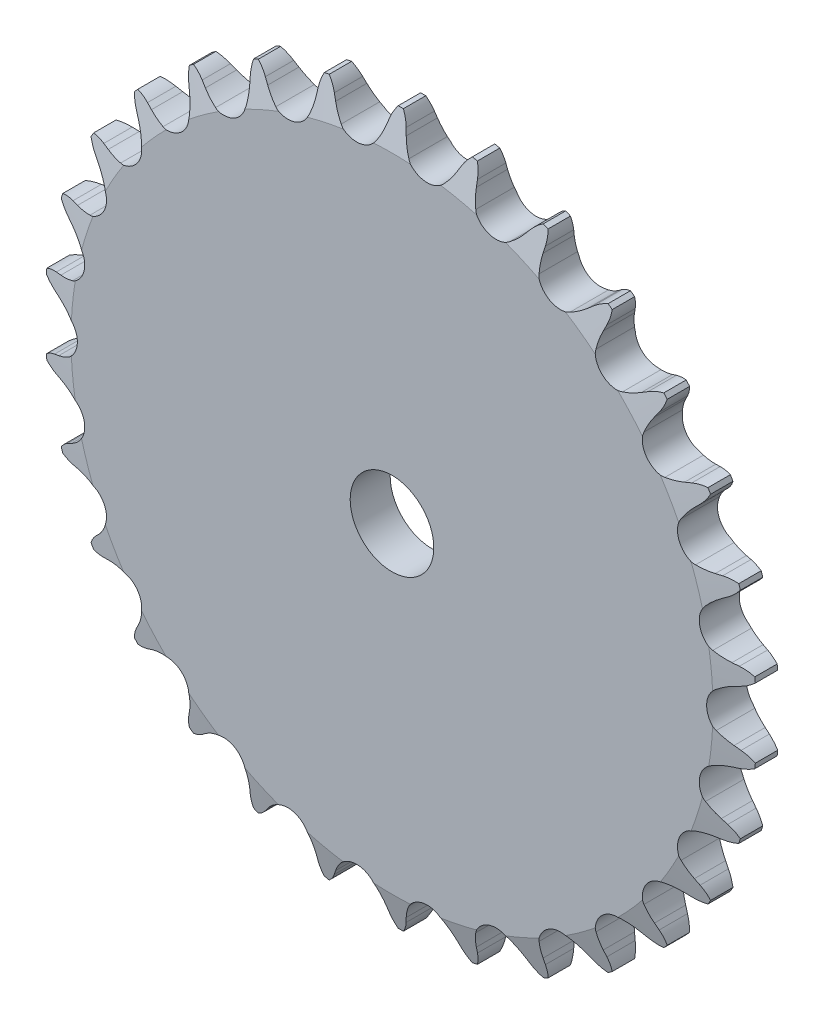
SolidWorks part; units mm, degrees
ref_plane "Front Plane" through (0, 0, 0) normal (0, 0, 1) x (1, 0, 0)
ref_plane "Top Plane" through (0, 0, 0) normal (0, 1, 0) x (1, 0, 0)
ref_plane "Right Plane" through (0, 0, 0) normal (1, 0, 0) x (0, 0, -1)
sketch "Sketch0" plane through (0, 0, 0) normal (0, 0, 1) x (1, 0, 0)
  line L0 (6.35, -60.4162) -> (0, 0) construction
  line L1 (0, 0) -> (18.7725, -57.7757) construction
  line L2 (0, 0) -> (-6.35, -60.4162) construction
  line L3 (6.35, -60.4162) -> (18.7725, -57.7757) construction
  line L4 (6.35, -60.4162) -> (-6.35, -60.4162) construction
  line L5 (11.4455, -61.0259) -> (10.9552, -60.0581)
  line L6 (6.35, -60.4162) -> (0, -61.0836) construction
  line L7 (1.4926, -62.072) -> (1.771, -61.0234)
  line L8 (0, -60.4162) -> (0, -64.2262) construction
  line L9 (9.2903, -57.6744) -> (1.7133, -64.74) construction
  line L10 (0, 0) -> (0, -60.4162) construction
  line L11 (10.9552, -60.0581) -> (1.7133, -64.74) construction
  line L12 (0, -64.2262) -> (0, -64.7904) construction
  line L13 (17.2023, -58.1095) -> (11.4455, -61.0259) construction
  circle A0 centre (0, 0) radius 64.2262 construction
  circle A1 centre (0, 0) radius 60.749 construction
  arc A2 (-5.25, -66.8497) -> (19.0341, -64.2974) centre (0, 0) ccw
  circle A3 centre (0, 0) radius 64.7904 construction
  circle A4 centre (6.35, -60.4162) radius 3.9624 construction
  arc A7 (9.2903, -57.6744) -> (2.9039, -58.3456) centre (6.35, -60.4162) ccw
  circle A8 centre (6.35, -60.4162) radius 4.0203 construction
  arc A9 (11.4455, -61.0259) -> (19.0341, -64.2974) centre (17.2023, -58.1095) ccw
  arc A10 (10.9552, -60.0581) -> (9.2903, -57.6744) centre (1.7133, -64.74) ccw
  arc A11 (1.4926, -62.072) -> (-5.25, -66.8497) centre (-4.7447, -60.4162) cw
  arc A12 (1.771, -61.0234) -> (2.9039, -58.3456) centre (11.7843, -63.6815) cw
  dimension "D1" = 4.0203
  dimension "Dr" = 7.9248
  dimension "Ds" = 8.0406
  dimension "R" = 4.0203
  dimension "Pitch" = 12.7
  dimension "A" = 37
  dimension "360/N" = 12
  dimension "B" = 16.133
  dimension "ab" = 11.0947
  dimension "J" = 3.81
  dimension "ac" = 6.3398
sketch "Sketch1" plane through (0, 0, 0) normal (1, 0, 0) x (0, 0, -1)
  line L0 (3.6068, 0) -> (-3.6068, 0)
  line L1 (-3.6068, 0) -> (-3.6068, 57.8762)
  line L2 (-3.6068, 57.8762) -> (-2.0193, 64.2262)
  line L3 (-2.0193, 64.2262) -> (2.0193, 64.2262)
  line L4 (2.0193, 64.2262) -> (3.6068, 57.8762)
  line L5 (3.6068, 57.8762) -> (3.6068, 0)
  line L7 (0, 64.2262) -> (0, 0) construction
  line L8 (-3.6068, 57.8762) -> (3.6068, 57.8762) construction
  line L9 (0, 64.2262) -> (0, -64.2262) construction
  line L10 (-3.6068, 57.8762) -> (-3.6068, 64.2262) construction
  line L11 (-3.6068, 64.2262) -> (-2.0193, 64.2262) construction
  line L12 (2.0193, 64.2262) -> (3.6068, 64.2262) construction
  line L13 (3.6068, 64.2262) -> (3.6068, 57.8762) construction
  dimension "t" = 7.2136
  dimension "g" = 1.5875
  dimension "h" = 6.35
revolve "Revolve1" add sketch "Sketch1" angle 360 mid plane about L0
extrude "Cut-Extrude1" cut sketch "Sketch0" against normal through all and the other way through all
pattern_circular "CirPattern1" count 30 over 360 about axis through (0, 0, 0) along (0, 0, 1) of "Cut-Extrude1"
sketch "Sketch2" plane through (0, 0, 0) normal (0, 0, 1) x (1, 0, 0)
  circle A0 centre (0, 0) radius 7.5406 construction
  circle A1 centre (0, 0) radius 30.1625
  circle A2 centre (0, 0) radius 64.262 construction
  dimension "Bore" = 15.0812
  dimension "Hub Dia." = 60.325
  dimension "OD" = 128.524
sketch "Sketch3" plane through (0, 0, 0) normal (0, 0, 1) x (1, 0, 0)
  circle A0 centre (0, 0) radius 7.5406 construction
  circle A1 centre (0, 0) radius 7.5406
  circle A2 centre (0, 0) radius 64.262 construction
  circle A3 centre (0, 0) radius 64.262
extrude "Cut-Extrude2" cut sketch "Sketch3" along normal through all and the other way through all flip side to cut
equation "\"360/N@Sketch0\" = 360/\"Teeth@CirPattern1\""
equation "\"Ds@Sketch0\" = 1.005 * \"Dr@Sketch0\" + 0.003"
equation "\"R@Sketch0\" = 1/2 * \"Ds@Sketch0\""
equation "\"A@Sketch0\" = 35 +  ( 60 / \"Teeth@CirPattern1\" ) "
equation "\"B@Sketch0\" = 18 -  ( 56 / \"Teeth@CirPattern1\" )"
equation "\"ac@Sketch0\" = 0.8 * \"Dr@Sketch0\""
equation "\"ab@Sketch0\" = 1.4 * \"Dr@Sketch0\""
equation "\"J@Sketch0\" = 0.3 * \"Pitch@Sketch0\""
equation "\"h@Sketch1\" = \"Pitch@Sketch0\" / 2"
equation "\"g@Sketch1\" = \"h@Sketch1\" / 4"
